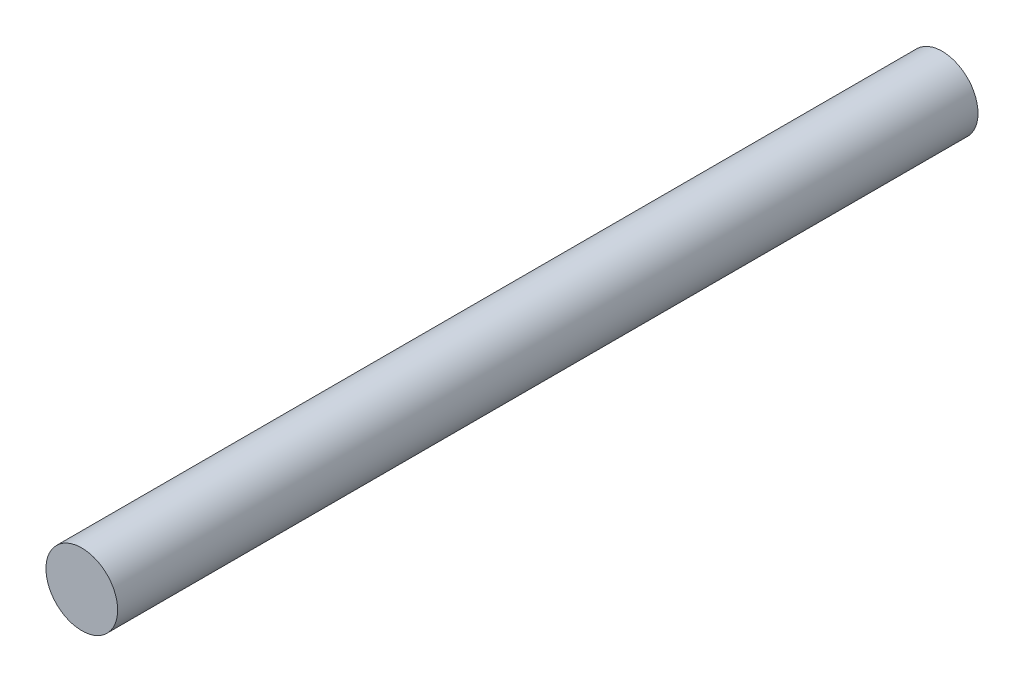
SolidWorks part; units mm, degrees
material "Plain Carbon Steel"
ref_plane "Front Plane" through (0, 0, 0) normal (0, 0, 1) x (1, 0, 0)
ref_plane "Top Plane" through (0, 0, 0) normal (0, 1, 0) x (1, 0, 0)
ref_plane "Right Plane" through (0, 0, 0) normal (1, 0, 0) x (0, 0, -1)
sketch "Sketch1" plane through (0, 0, 0) normal (0, 0, 1) x (1, 0, 0)
  circle A0 centre (0, 0) radius 6.35
  dimension "D1" = 12.7
extrude "Boss-Extrude1" add sketch "Sketch1" along normal blind 152.4
